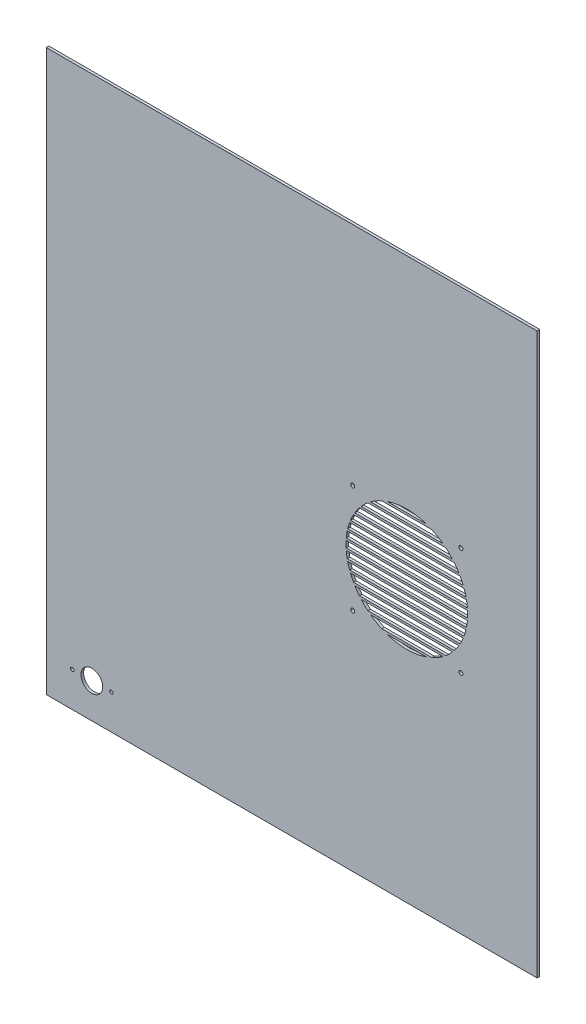
SolidWorks part; units mm, degrees
ref_plane "Přední rovina" through (0, 0, 0) normal (0, 0, 1) x (1, 0, 0)
ref_plane "Horní rovina" through (0, 0, 0) normal (0, 1, 0) x (1, 0, 0)
ref_plane "Pravá rovina" through (0, 0, 0) normal (1, 0, 0) x (0, 0, -1)
sketch "Skica1" plane through (0, 0, 0) normal (0, 0, 1) x (1, 0, 0)
  line L0 (222.9121, -56.25) -> (32.6147, -56.25)
  line L1 (-282.5, 322.5) -> (282.5, 322.5)
  line L2 (-282.5, 322.5) -> (-282.5, -322.5)
  line L3 (-282.5, -322.5) -> (282.5, -322.5)
  line L4 (282.5, 322.5) -> (282.5, -322.5)
  line L5 (-282.5, 322.5) -> (282.5, -322.5) construction
  line L6 (-282.5, -322.5) -> (282.5, 322.5) construction
  line L7 (222.9121, -66.25) -> (32.6147, -66.25)
  line L8 (222.9121, -66.25) -> (222.9121, -63.75)
  line L9 (222.9121, -63.75) -> (32.6147, -63.75)
  line L10 (32.6147, -66.25) -> (32.6147, -63.75)
  line L11 (222.9121, -53.75) -> (32.6147, -53.75)
  line L12 (222.9121, -56.25) -> (222.9121, -53.75)
  line L13 (32.6147, -56.25) -> (32.6147, -53.75)
  line L14 (222.9121, -46.25) -> (32.6147, -46.25)
  line L15 (222.9121, -43.75) -> (32.6147, -43.75)
  line L16 (222.9121, -46.25) -> (222.9121, -43.75)
  line L17 (32.6147, -46.25) -> (32.6147, -43.75)
  line L18 (222.9121, -36.25) -> (32.6147, -36.25)
  line L19 (222.9121, -33.75) -> (32.6147, -33.75)
  line L20 (222.9121, -36.25) -> (222.9121, -33.75)
  line L21 (32.6147, -36.25) -> (32.6147, -33.75)
  line L22 (222.9121, -26.25) -> (32.6147, -26.25)
  line L23 (222.9121, -23.75) -> (32.6147, -23.75)
  line L24 (222.9121, -26.25) -> (222.9121, -23.75)
  line L25 (32.6147, -26.25) -> (32.6147, -23.75)
  line L26 (222.9121, -16.25) -> (32.6147, -16.25)
  line L27 (222.9121, -13.75) -> (32.6147, -13.75)
  line L28 (222.9121, -16.25) -> (222.9121, -13.75)
  line L29 (32.6147, -16.25) -> (32.6147, -13.75)
  line L30 (222.9121, -6.25) -> (32.6147, -6.25)
  line L31 (222.9121, -3.75) -> (32.6147, -3.75)
  line L32 (222.9121, -6.25) -> (222.9121, -3.75)
  line L33 (32.6147, -6.25) -> (32.6147, -3.75)
  line L34 (222.9121, 3.75) -> (32.6147, 3.75)
  line L35 (222.9121, 6.25) -> (32.6147, 6.25)
  line L36 (222.9121, 3.75) -> (222.9121, 6.25)
  line L37 (32.6147, 3.75) -> (32.6147, 6.25)
  line L38 (222.9121, 13.75) -> (32.6147, 13.75)
  line L39 (222.9121, 16.25) -> (32.6147, 16.25)
  line L40 (222.9121, 13.75) -> (222.9121, 16.25)
  line L41 (32.6147, 13.75) -> (32.6147, 16.25)
  line L42 (222.9121, 23.75) -> (32.6147, 23.75)
  line L43 (222.9121, 26.25) -> (32.6147, 26.25)
  line L44 (222.9121, 23.75) -> (222.9121, 26.25)
  line L45 (32.6147, 23.75) -> (32.6147, 26.25)
  line L46 (222.9121, 33.75) -> (32.6147, 33.75)
  line L47 (222.9121, 36.25) -> (32.6147, 36.25)
  line L48 (222.9121, 33.75) -> (222.9121, 36.25)
  line L49 (32.6147, 33.75) -> (32.6147, 36.25)
  line L50 (222.9121, 43.75) -> (32.6147, 43.75)
  line L51 (222.9121, 46.25) -> (32.6147, 46.25)
  line L52 (222.9121, 43.75) -> (222.9121, 46.25)
  line L53 (32.6147, 43.75) -> (32.6147, 46.25)
  line L54 (222.9121, 53.75) -> (32.6147, 53.75)
  line L55 (222.9121, 56.25) -> (32.6147, 56.25)
  line L56 (222.9121, 53.75) -> (222.9121, 56.25)
  line L57 (32.6147, 53.75) -> (32.6147, 56.25)
  line L58 (222.9121, 63.75) -> (32.6147, 63.75)
  line L59 (222.9121, 66.25) -> (32.6147, 66.25)
  line L60 (222.9121, 63.75) -> (222.9121, 66.25)
  line L61 (32.6147, 63.75) -> (32.6147, 66.25)
  circle A0 centre (132.5, 0) radius 70
  circle A1 centre (194.75, -62.25) radius 2.3
  circle A2 centre (70.25, -62.25) radius 2.3
  circle A3 centre (70.25, 62.25) radius 2.3
  circle A4 centre (194.75, 62.25) radius 2.3
  circle A5 centre (-252.5, -282.5) radius 2
  circle A6 centre (-230, -282.5) radius 12.5
  circle A7 centre (-207.5, -282.5) radius 2
  point P0 (0, 0)
  point P19 (132.5, 0)
  dimension "D3" = 140
  dimension "D6" = 4.6
  dimension "D8" = 62.25
  dimension "D13" = 4
  dimension "D14" = 25
  dimension "D15" = 22.5
  dimension "D16" = 22.5
  dimension "D18" = 30
  dimension "D1" = 565
  dimension "D2" = 645
  dimension "D4" = 322.5
  dimension "D5" = 150
  dimension "D7" = 62.25
  dimension "D10" = 2.5
  dimension "D11" = 66.25
  dimension "D17" = 40
  dimension "D12" = 14
  dimension "D9" = 4
extrude "Přidat vysunutím1" add sketch "Skica1" along normal blind 3 contours L4 L1 L2 L3 A4 L58 A0 L55 L56 L54 L51 L52 L50 L47 L48 L46 L43 L44 L42 L39 L40 L38 L35 L36 L34 L31 L32 L30 L27 L28 L26 L23 L24 L22 L19 L20 L18 L15 L16 L14 | L9 A0 L7 | L58 A0 L59 | A1 L9 A0 L7 L8 | A2 L9 L10 L7 A0 | A4 L58 L60 L59 A0 | A3 L58 A0 L59 L61 | L0 L13 L11 L12
